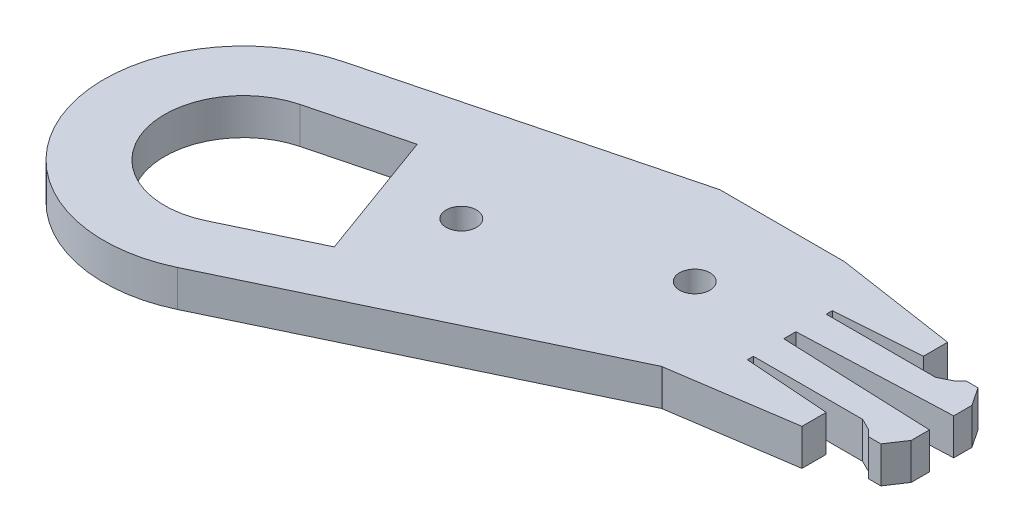
SolidWorks part; units mm, degrees
material "Lasercut ABS"
ref_plane "Front Plane" through (0, 0, 0) normal (0, 0, 1) x (1, 0, 0)
ref_plane "Top Plane" through (0, 0, 0) normal (0, 1, 0) x (1, 0, 0)
ref_plane "Right Plane" through (0, 0, 0) normal (1, 0, 0) x (0, 0, -1)
sketch "Sketch4" plane through (0, 0, 0) normal (0, 1, 0) x (1, 0, 0)
  line L0 (0, 0) -> (0, 17.2192) construction
  line L1 (-2.8794, 11.1337) -> (21.7373, 17.5)
  line L2 (4.9509, -10.3797) -> (31.9538, 2.5)
  line L3 (32, 2.5) -> (31.9538, 2.5)
  line L4 (32, 17.5) -> (21.7373, 17.5)
  arc A0 (-2.8794, 11.1337) -> (4.9509, -10.3797) centre (0, 0) ccw
  line B0 (6.0339, 8.2743) -> (9.9409, -2.46)
  line B1 (0, 0) -> (7.9874, 2.9072) construction
  line B2 (6.0339, 8.2743) -> (-1.6275, 6.293)
  line B3 (9.9409, -2.46) -> (2.7983, -5.8668)
  arc B4 (-1.6275, 6.293) -> (2.7983, -5.8668) centre (0, 0) ccw
  circle B5 centre (13.1557, 4.7883) radius 1.25
  circle B6 centre (27.2511, 9.9186) radius 1.25
  line B7 (32, 10) -> (35, 10) construction
  line B8 (35, 10.5) -> (35, 9.5)
  line B9 (35, 10.5) -> (47.5, 11)
  line B10 (47.5, 11) -> (47.5, 12.5)
  line B11 (47.5, 12.5) -> (46.5, 14)
  line B12 (46.5, 14) -> (45.5, 14)
  line B13 (45.5, 14) -> (45, 13.5)
  line B14 (45, 13.5) -> (44, 13)
  line B15 (44, 13) -> (35, 13)
  line B16 (35, 13) -> (35, 13.5)
  line B17 (35, 13.5) -> (42, 14)
  line B18 (42, 14) -> (42, 16)
  line B19 (42, 16) -> (32, 17.5)
  line B20 (35, 9.5) -> (47.5, 9)
  line B21 (47.5, 9) -> (47.5, 7.5)
  line B22 (47.5, 7.5) -> (46.5, 6)
  line B23 (46.5, 6) -> (45.5, 6)
  line B24 (45.5, 6) -> (45, 6.5)
  line B25 (45, 6.5) -> (44, 7)
  line B26 (44, 7) -> (35, 7)
  line B27 (35, 7) -> (35, 6.5)
  line B28 (35, 6.5) -> (42, 6)
  line B29 (42, 6) -> (42, 4)
  line B30 (42, 4) -> (32, 2.5)
  dimension "D1" = 70
  dimension "D2" = 5
  dimension "D3" = 10
  dimension "D4" = 42
sketch_block_instance "Block-Horn-TowerPro-1"
sketch_block "Block1" parameters "D1"=6.5, "D4"=2.5, "D2"=15, "D3"=11, "D5"=14, "D6"=15
sketch_block_instance "Block-Snap-Textile-1"
sketch_block "Block-Snap-Textile" parameters "D1"=3, "D2"=1, "D3"=2, "D4"=1.5, "D5"=10, "D6"=0.5, "D7"=9, "D8"=1, "D9"=0.5, "D10"=0.5, "D11"=0.5, "D12"=1, "D13"=12.5, "D14"=0.5, "D15"=0.5, "D16"=1.5, "D17"=1.5
extrude "Boss-Extrude2" add sketch "Sketch4" against normal blind 3 contours L0 A0 L2 L3 B30 B29 B28 B27 B26 B25 B24 B23 B22 B21 B20 B8 B9 B10 B11 B12 B13 B14 B15 B16 B17 B18 B19 L4 L1 B2 B0 B3 B4 B6 B5 | A0 L0 B4 B2 L1
sketch "Sketch5" plane through (0, -3, 0) normal (0, 1, 0) x (1, 0, 0)
  line L0 (4.6595, 12.0505) -> (20.1499, 16.0566) construction
  line L1 (10.4563, -3.876) -> (24.8976, 3.0121) construction
  line L2 (6.0339, 8.2743) -> (9.9409, -2.46) construction
  line L3 (-2.8794, 11.1337) -> (21.7373, 17.5) construction
  line L4 (4.9509, -10.3797) -> (31.9538, 2.5) construction
  text T0 "ONO V2" font "1CamBam_Stick_3" height 2.5
  text T1 "M8\r\n" font "1CamBam_Stick_3" height 2.5
  dimension "D1" = 16
  dimension "D2" = 1
  dimension "D3" = 3.5
equation "\"X\"= 10"
equation "\"Y\"= 42"
equation "\"D3@Sketch4\"=\"X\""
equation "\"D4@Sketch4\"=\"Y\""
